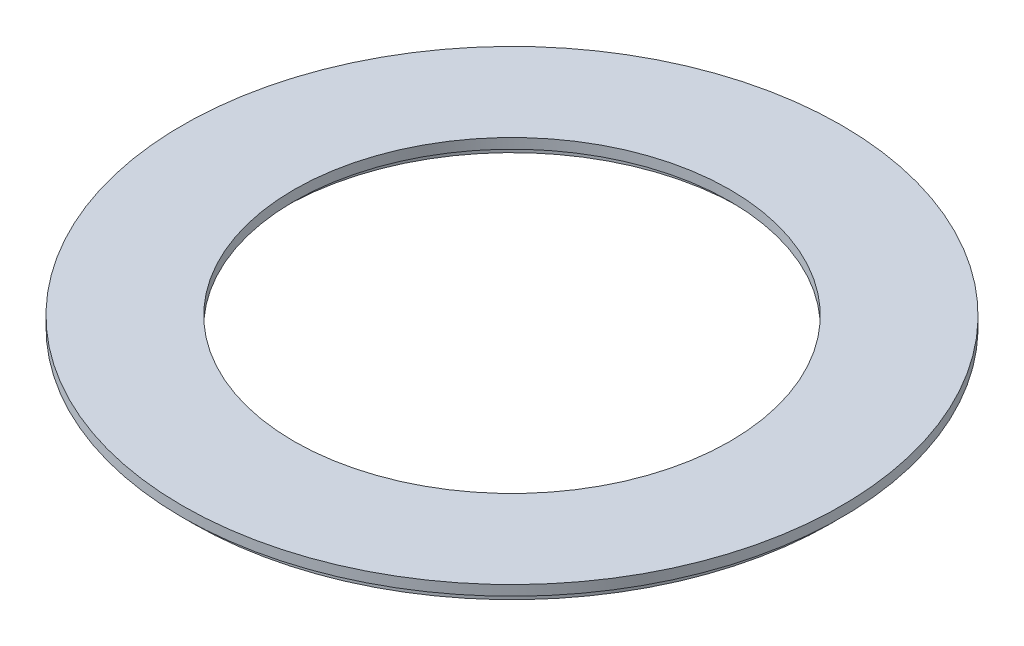
SolidWorks part; units mm, degrees
ref_plane "Front Plane" through (0, 0, 0) normal (0, 0, 1) x (1, 0, 0)
ref_plane "Top Plane" through (0, 0, 0) normal (0, 1, 0) x (1, 0, 0)
ref_plane "Right Plane" through (0, 0, 0) normal (1, 0, 0) x (0, 0, -1)
sketch "Sketch1" plane through (0, 0, 0) normal (0, 1, 0) x (1, 0, 0)
  circle A0 centre (0, 0) radius 16.25
  circle A1 centre (0, 0) radius 10.75
  dimension "D1" = 32.5
  dimension "D2" = 21.5
extrude "Boss-Extrude1" add sketch "Sketch1" along normal blind 0.5
sketch "Sketch2" plane through (0, 0, 0) normal (0, -1, 0) x (1, 0, 0)
  circle A0 centre (0, 0) radius 11.25
  circle A1 centre (0, 0) radius 15.75
  circle A2 centre (0, 0) radius 10.75 construction
  circle A3 centre (0, 0) radius 16.25 construction
  dimension "D1" = 0.5
  dimension "D2" = 0.5
extrude "Boss-Extrude2" add sketch "Sketch2" along normal blind 0.5
